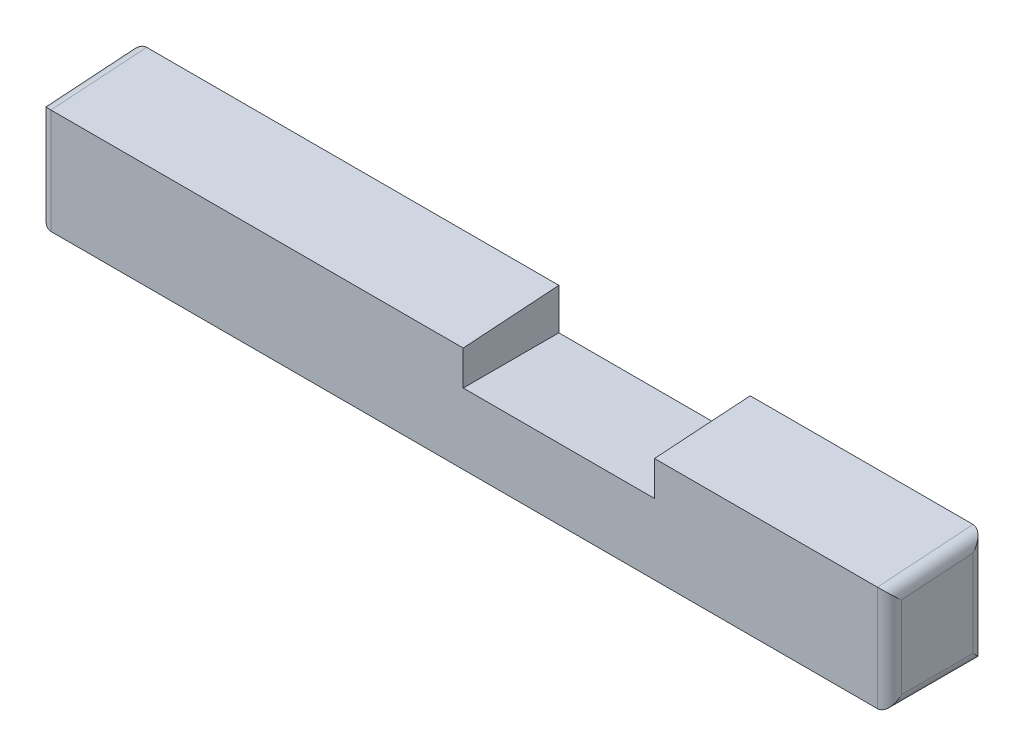
SolidWorks part; units mm, degrees
material "AISI 4340 Steel, normalized"
ref_plane "Front Plane" through (0, 0, 0) normal (0, 0, 1) x (1, 0, 0)
ref_plane "Top Plane" through (0, 0, 0) normal (0, 1, 0) x (1, 0, 0)
ref_plane "Right Plane" through (0, 0, 0) normal (1, 0, 0) x (0, 0, -1)
sketch "Sketch1" plane through (0, 0, 0) normal (1, 0, 0) x (0, 0, -1)
  line L0 (-0.1228, -2.0262) -> (-0.1228, 0.1738)
  line L1 (-0.1228, 0.1738) -> (1.8772, 0.3097)
  line L2 (1.8772, 0.3097) -> (1.8772, -2.0262)
  line L3 (1.8772, -2.0262) -> (-0.1228, -2.0262)
  dimension "D1" = 2.2
  dimension "D2" = 2
  dimension "D3" = 2.3359
extrude "Boss-Extrude3" add sketch "Sketch1" along normal mid plane 18.5 contours L1 L2 L3 L0
sketch "Sketch5" plane through (0, 0, -1.8772) normal (0, 0, -1) x (-1, 0, 0)
  line L0 (-4.34, 0.3097) -> (-4.34, -0.5503)
  line L1 (-9.25, 0.3097) -> (9.25, 0.3097) construction
  line L2 (-4.34, -0.5503) -> (-0.34, -0.5503)
  line L3 (-0.34, -0.5503) -> (-0.34, 0.3097)
  line L4 (-0.34, 0.3097) -> (-4.34, 0.3097)
  dimension "D1" = 4.91
  dimension "D2" = 0.86
  dimension "D3" = 4
extrude "Cut-Extrude1" cut sketch "Sketch5" against normal blind 2
sketch "Sketch6" plane through (0, -2.0262, 0) normal (0, -1, 0) x (1, 0, 0)
  line L0 (9.25, -1.8772) -> (-9.25, -1.8772) construction
  line L1 (-1.41, -0.6272) -> (2.09, -0.6272)
  line L2 (-1.41, -0.6272) -> (-1.41, -1.1272)
  line L3 (-1.41, -1.1272) -> (2.09, -1.1272)
  line L4 (2.09, -0.6272) -> (2.09, -1.1272)
  line L5 (9.25, 0.1228) -> (-9.25, 0.1228) construction
  line L6 (-9.25, -1.8772) -> (-9.25, 0.1228) construction
  line L8 (9.25, -1.8772) -> (9.25, 0.1228) construction
  point P12 (2.09, -0.8772)
  dimension "D1" = 7.16
  dimension "D2" = 0.5
  dimension "D3" = 0.75
  dimension "D4" = 0.75
  dimension "D5" = 7.84
extrude "Boss-Extrude4" add sketch "Sketch6" along normal blind 0.5
sketch "Sketch7" plane through (0, 0, -1.8772) normal (0, 0, -1) x (-1, 0, 0)
  line L0 (9.25, 0.3097) -> (8.53, 0.3097)
  line L1 (-0.34, 0.3097) -> (9.25, 0.3097) construction
  line L2 (8.53, 0.3097) -> (8.53, -2.0262)
  line L3 (-9.25, -2.0262) -> (9.25, -2.0262) construction
  line L4 (8.53, -2.0262) -> (9.25, -2.0262)
  line L5 (9.25, -2.0262) -> (9.25, 0.3097)
  dimension "D1" = 0.72
extrude "Cut-Extrude2" cut sketch "Sketch7" against normal blind 2
fillet "Fillet1" radius 0.25 8 edges at (9.25, 0.2417, -0.8772) (9.25, -0.8583, -1.8772) (9.25, -2.0262, -0.8772) (9.25, -0.9262, 0.1228) (-8.53, -0.9262, 0.1228) (-8.53, -2.0262, -0.8772) (-8.53, -0.8583, -1.8772) (-8.53, 0.2417, -0.8772)
fillet "Fillet2" radius 0.1 2 edges at (2.09, -2.5262, -0.8772) (-1.41, -2.5262, -0.8772)
